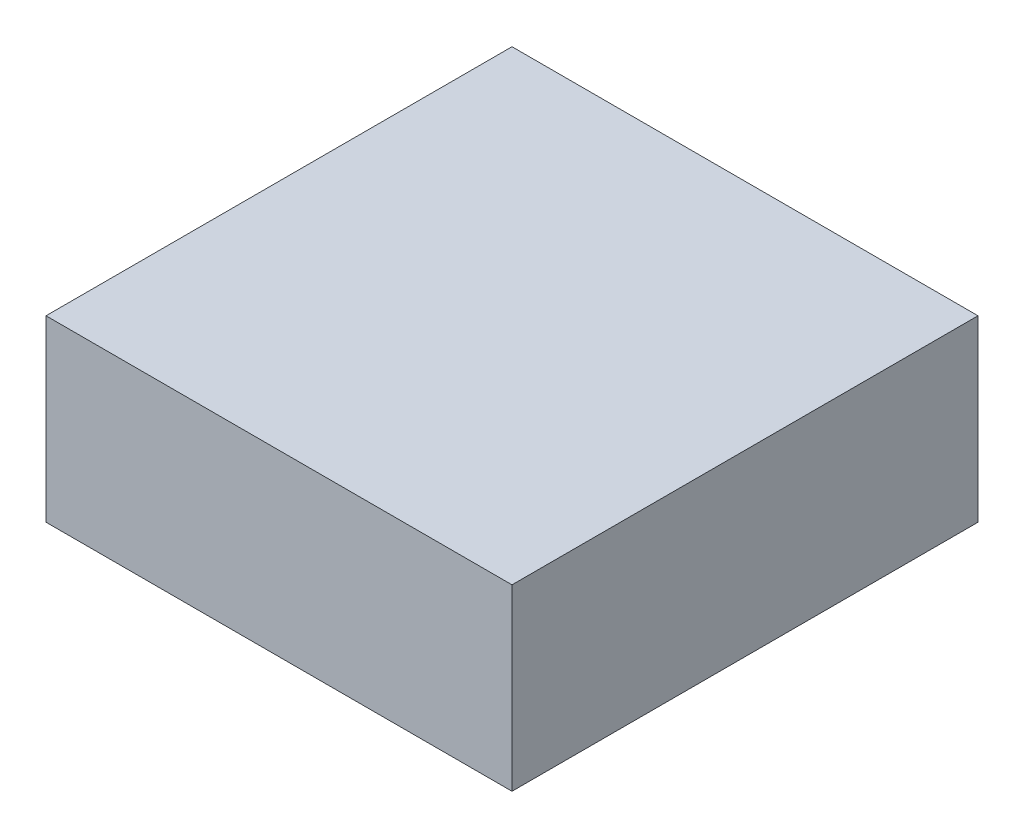
SolidWorks part; units mm, degrees
ref_plane "Front Plane" through (0, 0, 0) normal (0, 0, 1) x (1, 0, 0)
ref_plane "Top Plane" through (0, 0, 0) normal (0, 1, 0) x (1, 0, 0)
ref_plane "Right Plane" through (0, 0, 0) normal (1, 0, 0) x (0, 0, -1)
sketch "Sketch2" plane through (0, 0, 0) normal (0, 0, 1) x (1, 0, 0)
  line L0 (-2750, 2000) -> (-7000, 2000)
  line L2 (-2750, 2000) -> (-2750, 2732.3741)
  line L3 (-2750, 2732.3741) -> (-2123.3813, 3332)
  line L4 (-2123.3813, 3332) -> (0, 3332)
  line L5 (0, 3332) -> (0, 3372)
  line L6 (0, 3372) -> (-7000, 3372)
  line L7 (-7000, 3372) -> (-7000, 2000)
  dimension "D1" = 3332
  dimension "D2" = 7000
  dimension "D3" = 40
  dimension "D4" = 2000
  dimension "D8" = 2750
ref_axis "Axis1" through (0, 3520.44, 0) along (0, -1, 0)
revolve "Revolve2" add sketch "Sketch2" angle 360 about axis through (0, 3520.44, 0) along (0, -1, 0)
sketch "Sketch3" plane through (0, 3372, 0) normal (0, 1, 0) x (1, 0, 0)
  line L1 (-7000, 7000) -> (7000, 7000)
  line L2 (-7000, 7000) -> (-7000, -7000)
  line L3 (-7000, -7000) -> (7000, -7000)
  line L4 (7000, 7000) -> (7000, -7000)
  circle A0 centre (0, 0) radius 7000 construction
  circle A1 centre (0, 0) radius 6104.3847
  circle M5 centre (0, 0) radius 7000
extrude "Boss-Extrude1" add sketch "Sketch3" against normal up to surface (1372 mm away) contours L2 L3 M5 | L1 L2 M5 | L4 L1 M5 | L4 L3 M5 up to face at (0, 2000, 2750)
sketch "Sketch4" plane through (0, 2000, 0) normal (0, -1, 0) x (1, 0, 0)
  line L1 (-7000, 7000) -> (7000, 7000)
  line L2 (-7000, 7000) -> (-7000, -7000)
  line L3 (-7000, -7000) -> (7000, -7000)
  line L4 (7000, 7000) -> (7000, -7000)
  circle A0 centre (0, 0) radius 5000
  dimension "D1" = 10000
extrude "Boss-Extrude2" add sketch "Sketch4" along normal blind 4000
